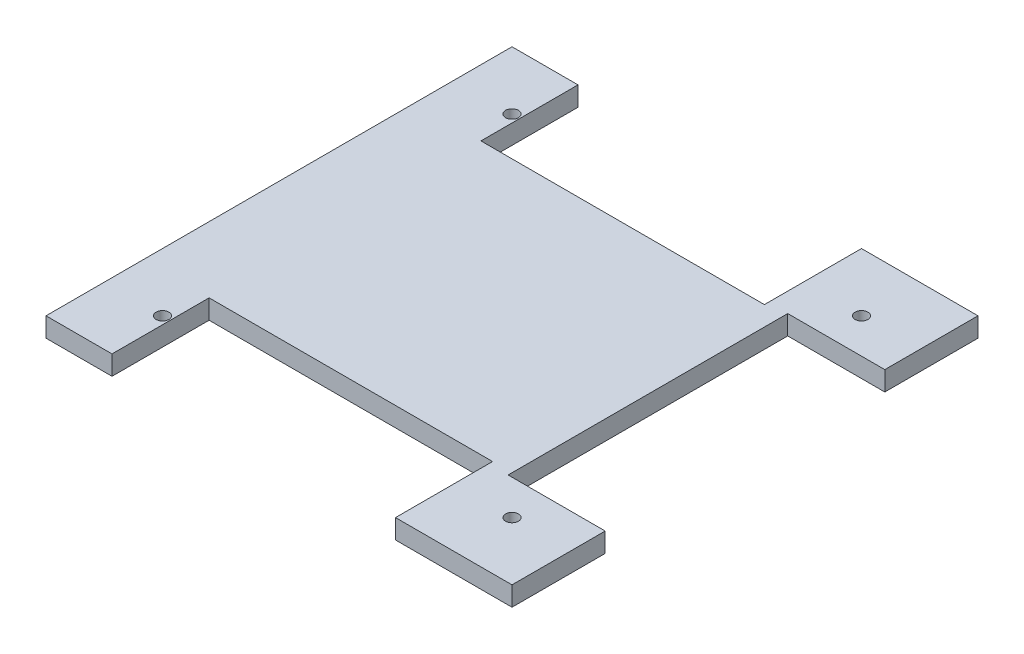
SolidWorks part; units mm, degrees
ref_plane "Front" through (0, 0, 0) normal (0, 0, 1) x (1, 0, 0)
ref_plane "Top" through (0, 0, 0) normal (0, 1, 0) x (1, 0, 0)
ref_plane "Right" through (0, 0, 0) normal (1, 0, 0) x (0, 0, -1)
sketch "Sketch1" plane through (0, 0, 0) normal (0, 1, 0) x (1, 0, 0)
  line L0 (-43, 60) -> (-43, 35)
  line L1 (-60, -60) -> (-43, -60)
  line L2 (-60, -60) -> (-60, 60)
  line L3 (-60, 60) -> (-43, 60)
  line L4 (60, -60) -> (60, -36)
  line L5 (-60, -60) -> (60, 60) construction
  line L6 (-60, 60) -> (60, -60) construction
  line L7 (-43, 35) -> (30, 35)
  line L8 (30, 35) -> (30, 60)
  line L9 (30, 60) -> (60, 60)
  line L10 (60, 36) -> (35, 36)
  line L11 (35, 36) -> (35, -36)
  line L12 (35, -36) -> (60, -36)
  line L13 (60, 36) -> (60, 60)
  line L14 (-43, -60) -> (-43, -35)
  line L15 (-43, -35) -> (30, -35)
  line L16 (30, -35) -> (30, -60)
  line L17 (30, -60) -> (60, -60)
  point P0 (0, 0)
  dimension "D1" = 120
  dimension "D2" = 120
  dimension "D3" = 17
  dimension "D4" = 25
  dimension "D5" = 25
  dimension "D6" = 30
  dimension "D7" = 25
  dimension "D8" = 24
  dimension "D9" = 24
extrude "Boss-Extrude1" add sketch "Sketch1" along normal blind 5
hole_wizard "Ø3.3 (3.3) Diameter Hole1" positions "Sketch3" profile "Sketch2" hole size "Ø3.3" standard "ANSI Metric" end condition through all
sketch "Sketch3" plane through (0, 5, 0) normal (0, 1, 0) x (1, 0, 0)
  line L1 (-45, -45) -> (45, -45)
  line L2 (-45, -45) -> (-45, 45)
  line L3 (-45, 45) -> (45, 45)
  line L4 (45, -45) -> (45, 45)
  line L5 (-45, -45) -> (45, 45) construction
  line L6 (-45, 45) -> (45, -45) construction
  line L7 (-60, 60) -> (-60, -60) construction
  line L8 (-60, -60) -> (-43, -60) construction
  point P0 (-45, 45)
  point P2 (45, 45)
  point P4 (45, -45)
  point P6 (-45, -45)
  dimension "D1" = 90
  dimension "D2" = 90
  dimension "D3" = 15
  dimension "D4" = 15
sketch "Sketch2" plane through (-45, 5, -45) normal (1, 0, 0) x (0, 0, 1)
  line L0 (0, 0) -> (0, 5)
  line L1 (0, 5) -> (1.65, 5)
  line L2 (1.65, 5) -> (1.65, 0)
  line L5 (1.65, 0) -> (0, 0)
  line L11 (0, -6.35) -> (0, 107.95) construction
  dimension "Thru Hole Dia." = 3.3
  dimension "Thru Hole Depth" = 5
